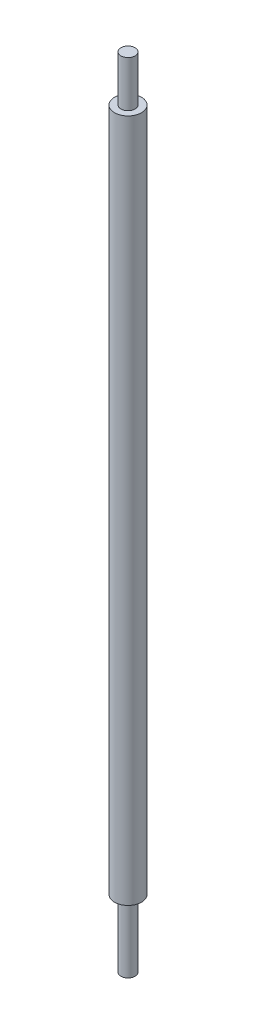
SolidWorks part; units mm, degrees
ref_plane "Спереди" through (0, 0, 0) normal (0, 0, 1) x (1, 0, 0)
ref_plane "Сверху" through (0, 0, 0) normal (0, 1, 0) x (1, 0, 0)
ref_plane "Справа" through (0, 0, 0) normal (1, 0, 0) x (0, 0, -1)
sketch "Эскиз1" plane through (0, 0, 0) normal (0, 1, 0) x (1, 0, 0)
  circle A0 centre (0, 0) radius 7.6
  dimension "D1" = 15.2
extrude "Бобышка-Вытянуть1" add sketch "Эскиз1" along normal blind 450
sketch "Эскиз2" plane through (0, 450, 0) normal (0, 1, 0) x (1, 0, 0)
  circle A0 centre (0, 0) radius 4
  circle A1 centre (0, 0) radius 7.6
  dimension "D1" = 8
extrude "Вырез-Вытянуть1" cut sketch "Эскиз2" against normal blind 26
sketch "Эскиз3" plane through (0, 0, 0) normal (0, -1, 0) x (1, 0, 0)
  circle A0 centre (0, 0) radius 4
  circle A1 centre (0, 0) radius 7.6
  dimension "D1" = 8
extrude "Вырез-Вытянуть2" cut sketch "Эскиз3" against normal blind 38
